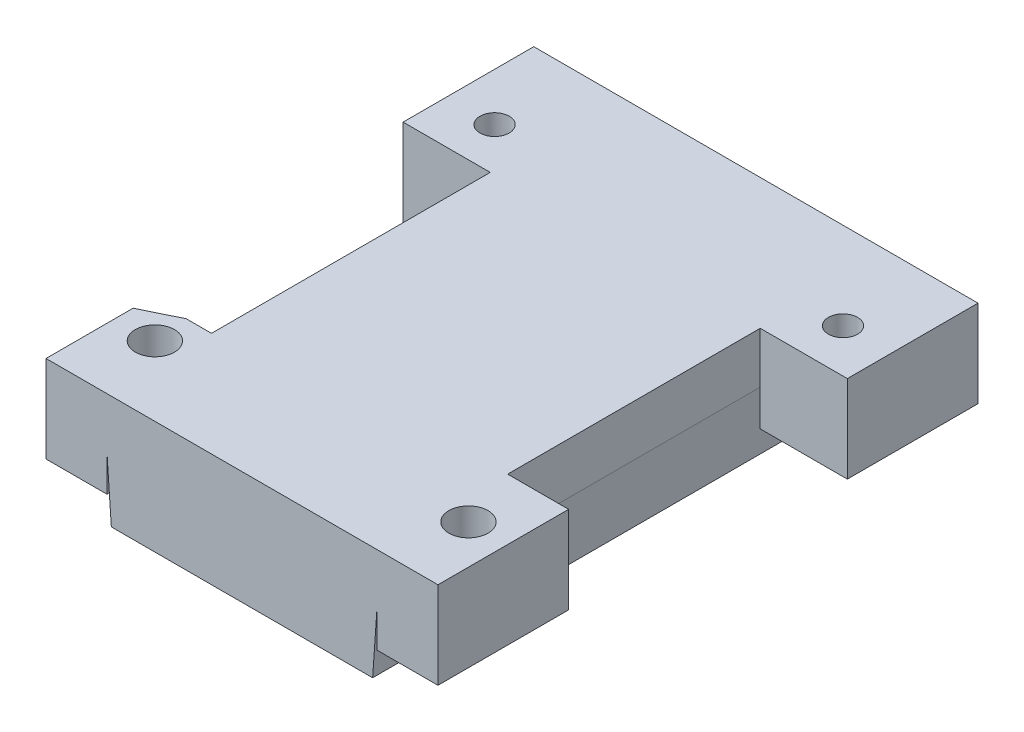
SolidWorks part; units mm, degrees
ref_plane "Front Plane" through (0, 0, 0) normal (0, 0, 1) x (1, 0, 0)
ref_plane "Top Plane" through (0, 0, 0) normal (0, 1, 0) x (1, 0, 0)
ref_plane "Right Plane" through (0, 0, 0) normal (1, 0, 0) x (0, 0, -1)
sketch "Sketch1" plane through (0, 0, 0) normal (0, 1, 0) x (1, 0, 0)
  line L0 (-23, 32) -> (-23, 22)
  line L1 (0, 0) -> (-26, 0)
  line L2 (0, 0) -> (0, 53)
  line L3 (0, 53) -> (-26, 53)
  line L4 (-26, 0) -> (-26, 53)
  line L5 (-23, 48) -> (-3, 48)
  line L6 (-23, 48) -> (-23, 38)
  line L7 (-23, 38) -> (-3, 38)
  line L8 (-3, 48) -> (-3, 38)
  line L9 (-23, 32) -> (-3, 32)
  line L10 (-3, 32) -> (-3, 22)
  line L11 (-23, 22) -> (-3, 22)
  line L12 (-23, 16) -> (-23, 6)
  line L13 (-23, 16) -> (-3, 16)
  line L14 (-3, 16) -> (-3, 6)
  line L15 (-23, 6) -> (-3, 6)
  point P9 (-13, 48)
  point P10 (-13, 53)
  dimension "D1" = 26
  dimension "D2" = 53
  dimension "D3" = 20
  dimension "D4" = 10
  dimension "D5" = 5
  dimension "D6" = 3
extrude "Boss-Extrude1" add sketch "Sketch1" along normal blind 5
sketch "Sketch2" plane through (0, 5, 0) normal (0, 1, 0) x (1, 0, 0)
  line L17 (-26, 53) -> (0, 53)
  line L18 (-26, 53) -> (-26, 0)
  line L19 (-26, 0) -> (0, 0)
  line L20 (0, 53) -> (0, 0)
  line L21 (-28.5, 56) -> (2.5, 56)
  line L22 (-28.5, 56) -> (-28.5, -3)
  line L23 (-28.5, -3) -> (2.5, -3)
  line L24 (2.5, 56) -> (2.5, -3)
  dimension "D1" = 3
  dimension "D2" = 2.5
  dimension "D3" = 2.5
  dimension "D4" = 3
extrude "Boss-Extrude2" add sketch "Sketch2" against normal blind 10
sketch "Sketch3" plane through (0, 5, 0) normal (0, 1, 0) x (1, 0, 0)
  line L1 (-28.5, 56) -> (2.5, 56)
  line L2 (-28.5, 56) -> (-28.5, -3)
  line L3 (-28.5, -3) -> (2.5, -3)
  line L4 (2.5, 56) -> (2.5, -3)
extrude "Boss-Extrude3" add sketch "Sketch3" along normal blind 3
sketch "Sketch4" plane through (0, 8, 0) normal (0, 1, 0) x (1, 0, 0)
  line L1 (-5, 56) -> (-11, 56)
  line L2 (-5, 56) -> (-5, 10)
  line L3 (-5, 10) -> (-11, 10)
  line L4 (-11, 56) -> (-11, 10)
  line L6 (-3, 38) -> (-3, 48) construction
  line L8 (-28.5, -3) -> (2.5, -3) construction
  dimension "D1" = 6
  dimension "D2" = 2
  dimension "D3" = 46
  dimension "D4" = 13
extrude "Boss-Extrude4" [suppressed] add sketch "Sketch4" along normal blind 55
sketch "Sketch5" [suppressed] plane through (-5, 0, 0) normal (1, 0, 0) x (0, 0, -1)
  line L0 (10, 8) -> (56, 8) construction
  line L1 (56, 63) -> (56, 8) construction
  line L2 (19, 48) -> (50, 17) construction
  line L3 (50, 48) -> (19, 17) construction
  circle A0 centre (50, 17) radius 1.75
  circle A1 centre (19, 17) radius 1.75
  circle A2 centre (19, 48) radius 1.75
  circle A3 centre (50, 48) radius 1.75
  circle A4 centre (34.5, 32.5) radius 13.5
  dimension "D2" = 6
  dimension "D3" = 3.5
  dimension "D6" = 27
  dimension "D1" = 9
  dimension "D4" = 2
  dimension "D5" = 2
extrude "Cut-Extrude1" [suppressed] cut sketch "Sketch5" against normal through all
chamfer "Chamfer1" distance 0.5 angle 86 2 edges at (2.5, -5, -26.5) (-28.5, -5, -26.5)
sketch "Sketch6" [suppressed] plane through (-5, 0, 0) normal (1, 0, 0) x (0, 0, -1)
  line L0 (10, 63) -> (10, 8) construction
  line L1 (56, 63) -> (10, 63)
  line L2 (56, 63) -> (56, 56)
  line L3 (56, 56) -> (10, 56)
  line L4 (10, 63) -> (10, 56)
  dimension "D1" = 7
extrude "Boss-Extrude5" [suppressed] add sketch "Sketch6" along normal blind 14
sketch "Sketch7" [suppressed] plane through (0, 63, 0) normal (0, 1, 0) x (1, 0, 0)
  line L0 (-11, 56) -> (-11, 10) construction
  line L1 (-8.5, 39.5) -> (-3.5, 39.5)
  line L2 (-8.5, 39.5) -> (-8.5, 34.5)
  line L3 (-8.5, 34.5) -> (-3.5, 34.5)
  line L4 (-3.5, 39.5) -> (-3.5, 34.5)
  line L5 (1.5, 39.5) -> (6.5, 39.5)
  line L6 (1.5, 39.5) -> (1.5, 34.5)
  line L7 (1.5, 34.5) -> (6.5, 34.5)
  line L8 (6.5, 39.5) -> (6.5, 34.5)
  line L9 (-8.5, 16.5) -> (-3.5, 16.5)
  line L10 (-8.5, 16.5) -> (-8.5, 11.5)
  line L11 (-8.5, 11.5) -> (-3.5, 11.5)
  line L12 (-3.5, 16.5) -> (-3.5, 11.5)
  line L13 (1.5, 16.5) -> (6.5, 16.5)
  line L14 (1.5, 16.5) -> (1.5, 11.5)
  line L15 (1.5, 11.5) -> (6.5, 11.5)
  line L16 (6.5, 16.5) -> (6.5, 11.5)
  line L17 (-11, 10) -> (9, 10) construction
  point P18 (-6, 16.5)
  point P19 (-6, 39.5)
  point P20 (4, 39.5)
  point P21 (4, 16.5)
  point P22 (-3.5, 37)
  point P23 (1.5, 37)
  point P24 (-3.5, 14)
  point P25 (1.5, 14)
  dimension "D1" = 5
  dimension "D2" = 5
  dimension "D3" = 2.5
  dimension "D4" = 1.5
  dimension "D5" = 23
extrude "Cut-Extrude2" [suppressed] cut sketch "Sketch7" against normal blind 5
sketch "Sketch8" [suppressed] plane through (0, 0, -56) normal (0, 0, -1) x (-1, 0, 0)
  line L0 (-9, 56) -> (-9, 63) construction
  line L1 (-9, 8) -> (5.6893, 8)
  line L2 (-9, 8) -> (-9, 1)
  line L3 (-9, 1) -> (5.6893, 1)
  line L4 (5.6893, 8) -> (5.6893, 1)
  line L5 (-2.5, 8) -> (5, 8) construction
extrude "Boss-Extrude6" [suppressed] add sketch "Sketch8" against normal blind 7.5
sketch "Sketch9" [suppressed] plane through (0, 0, -56) normal (0, 0, -1) x (-1, 0, 0)
  line L0 (-9, 56) -> (-9, 63) construction
  line L1 (-9, 8) -> (-9, 1) construction
  line L2 (11, 63) -> (11, 8) construction
  line L3 (5, 56) -> (5, 8) construction
  line L4 (-9, 8) -> (5, 8) construction
  line L6 (-9, 56) -> (5, 56) construction
  circle A0 centre (-5.5, 59.5) radius 1.75
  circle A1 centre (-5.5, 4.5) radius 1.75
  circle A2 centre (8, 54) radius 1.75
  circle A3 centre (8, 10) radius 1.75
  circle A4 centre (8, 32) radius 1.75
  point P5 (-9, 59.5)
  point P9 (-9, 4.5)
  dimension "D1" = 3.5
  dimension "D2" = 3.5
  dimension "D3" = 3.5
  dimension "D4" = 3.5
  dimension "D5" = 3
  dimension "D6" = 3
  dimension "D7" = 3
  dimension "D8" = 2
  dimension "D9" = 2
  dimension "D10" = 22
  dimension "D11" = 22
extrude "Cut-Extrude3" [suppressed] cut sketch "Sketch9" against normal blind 4
sketch "Sketch10" plane through (0, 8, 0) normal (0, 1, 0) x (1, 0, 0)
  line L0 (-13, -3) -> (-13, 56) construction
  line L1 (2.5, -3) -> (9.5, -3)
  line L2 (2.5, -3) -> (2.5, 12)
  line L3 (2.5, 12) -> (9.5, 12)
  line L4 (9.5, -3) -> (9.5, 12)
  line L9 (-28.5, -3) -> (2.5, -3) construction
  line L10 (2.5, 56) -> (-28.5, 56) construction
  line L11 (-28.5, 12) -> (-35.5, 12)
  line L12 (-35.5, -3) -> (-35.5, 12)
  line L13 (-28.5, -3) -> (-35.5, -3)
  line L14 (-28.5, -3) -> (-28.5, 12)
  circle A0 centre (5, 5) radius 2.25
  circle A1 centre (-31, 5) radius 2.25
  dimension "D6" = 4.5
  dimension "D3" = 4.5
  dimension "D1" = 15
  dimension "D2" = 7
  dimension "D5" = 8
extrude "Boss-Extrude7" add sketch "Sketch10" against normal blind 10
sketch "Sketch11" plane through (0, 8, 0) normal (0, 1, 0) x (1, 0, 0)
  line L1 (-35.5, 12) -> (-28.5, 12)
  line L2 (-35.5, 12) -> (-35.5, 9)
  line L3 (-35.5, 9) -> (-28.5, 9)
  line L4 (-28.5, 12) -> (-28.5, 9)
  dimension "D1" = 3
extrude "Cut-Extrude4" cut sketch "Sketch11" against normal blind 10
chamfer "Chamfer2" distance 2 angle 64 1 edges at (-35.5, 3, -9)
sketch "Sketch12" plane through (0, 8, 0) normal (0, 1, 0) x (1, 0, 0)
  line L0 (2.5, 12) -> (2.5, 56) construction
  line L1 (2.5, 56) -> (-28.5, 56) construction
  line L2 (-13, 56) -> (-13, 17.5206) construction
  line L3 (2.5, 56) -> (12.5, 56)
  line L4 (2.5, 56) -> (2.5, 41)
  line L5 (2.5, 41) -> (12.5, 41)
  line L6 (12.5, 56) -> (12.5, 41)
  line L7 (-28.5, 41) -> (-38.5, 41)
  line L8 (-38.5, 56) -> (-38.5, 41)
  line L9 (-28.5, 56) -> (-38.5, 56)
  line L10 (-28.5, 56) -> (-28.5, 41)
  circle A0 centre (7, 46) radius 1.6764
  circle A1 centre (-33, 46) radius 1.6764
  dimension "D1" = 4.5
  dimension "D2" = 10
  dimension "D3" = 15
  dimension "D4" = 10
extrude "Boss-Extrude8" add sketch "Sketch12" against normal up to surface (10 mm away) up to face at (5, -2, -2.75)
